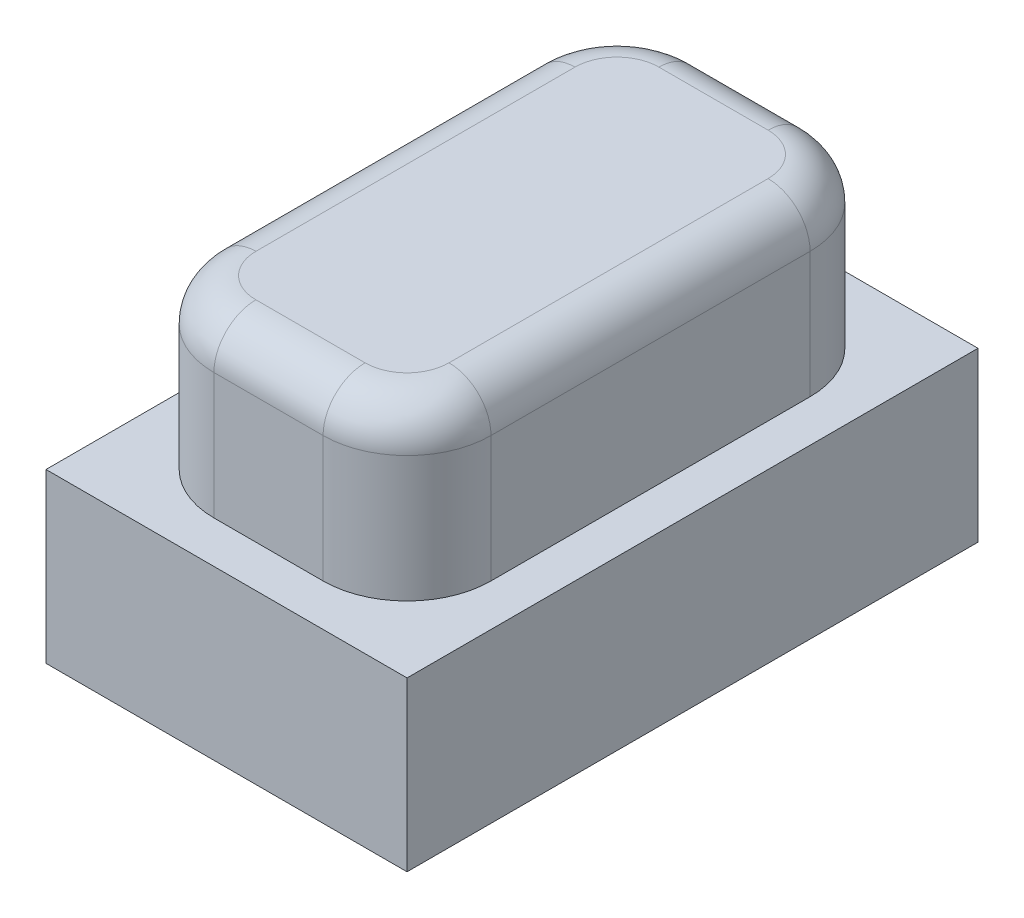
SolidWorks part; units mm, degrees
ref_plane "前视基准面" through (0, 0, 0) normal (0, 0, 1) x (1, 0, 0)
ref_plane "上视基准面" through (0, 0, 0) normal (0, 1, 0) x (1, 0, 0)
ref_plane "右视基准面" through (0, 0, 0) normal (1, 0, 0) x (0, 0, -1)
other "Configuration Table"
sketch "草图1" plane through (0, 0, 0) normal (0, 1, 0) x (1, 0, 0)
  line L1 (-0.65, -2.9) -> (0.65, -2.9)
  line L2 (-1.65, -1.9) -> (-1.65, 1.9)
  line L3 (-0.65, 2.9) -> (0.65, 2.9)
  line L4 (1.65, -1.9) -> (1.65, 1.9)
  line L5 (-1.65, -2.9) -> (1.65, 2.9) construction
  line L6 (-1.65, 2.9) -> (1.65, -2.9) construction
  arc A0 (0.65, -2.9) -> (1.65, -1.9) centre (0.65, -1.9) ccw
  arc A1 (-1.65, 1.9) -> (-0.65, 2.9) centre (-0.65, 1.9) cw
  arc A2 (-0.65, -2.9) -> (-1.65, -1.9) centre (-0.65, -1.9) cw
  arc A3 (0.65, 2.9) -> (1.65, 1.9) centre (0.65, 1.9) cw
  point P0 (0, 0)
  dimension "D3" = 1
  dimension "D1" = 3.3
  dimension "D2" = 5.8
extrude "凸台-拉伸1" add sketch "草图1" along normal blind 2
sketch "草图2" plane through (0, 0, 0) normal (0, -1, 0) x (1, 0, 0)
  line L5 (2.15, 3.4) -> (-2.15, 3.4)
  line L6 (2.15, 3.4) -> (2.15, -3.4)
  line L7 (2.15, -3.4) -> (-2.15, -3.4)
  line L8 (-2.15, 3.4) -> (-2.15, -3.4)
  line L9 (2.15, 3.4) -> (-2.15, -3.4) construction
  line L10 (2.15, -3.4) -> (-2.15, 3.4) construction
  point P0 (0, 0)
  dimension "D1" = 4.3
  dimension "D2" = 6.8
extrude "凸台-拉伸2" add sketch "草图2" along normal blind 1
sketch "草图4" plane through (0, -1, 0) normal (0, -1, 0) x (1, 0, 0)
  line L0 (-2.15, -3.4) -> (2.15, -3.4) construction
  line L1 (2.15, -3.4) -> (-2.15, -3.4)
  line L2 (2.15, -3.4) -> (2.15, 3.4)
  line L3 (2.15, 3.4) -> (-2.15, 3.4)
  line L4 (-2.15, -3.4) -> (-2.15, 3.4)
  line L5 (2.15, -3.4) -> (2.15, 3.4) construction
  line L6 (-2.15, 3.4) -> (-2.15, -3.4) construction
  line L7 (1.65, -2.9) -> (-1.65, -2.9)
  line L8 (-1.65, -2.9) -> (-1.65, 2.9)
  line L9 (1.65, 2.9) -> (-1.65, 2.9)
  line L10 (1.65, -2.9) -> (1.65, 2.9)
  dimension "D1" = 0.5
extrude "凸台-拉伸3" add sketch "草图4" along normal blind 1
fillet "圆角1" radius 0.5 8 edges at (-1.3571, 2, 2.6071) (-1.65, 2, 0) (-1.3571, 2, -2.6071) (0, 2, -2.9) (1.3571, 2, -2.6071) (1.65, 2, 0) (1.3571, 2, 2.6071) (0, 2, 2.9)
